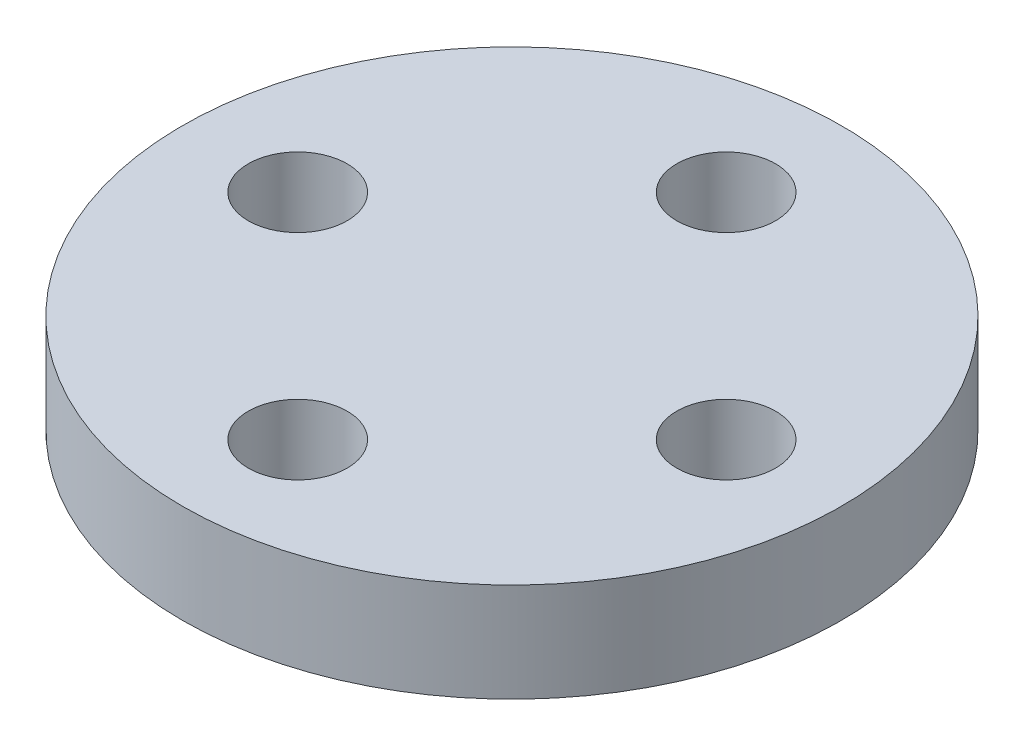
SolidWorks part; units mm, degrees
ref_plane "Front Plane" through (0, 0, 0) normal (0, 0, 1) x (1, 0, 0)
ref_plane "Top Plane" through (0, 0, 0) normal (0, 1, 0) x (1, 0, 0)
ref_plane "Right Plane" through (0, 0, 0) normal (1, 0, 0) x (0, 0, -1)
sketch "Sketch2" plane through (0, 0, 0) normal (0, 1, 0) x (1, 0, 0)
  circle A0 centre (0, 0) radius 10
  circle A7 centre (0, -6.5) radius 1.5
  circle A8 centre (-6.5, 0) radius 1.5
  circle A9 centre (0, 6.5) radius 1.5
  circle A10 centre (6.5, 0) radius 1.5
  dimension "D1" = 4
extrude "Boss-Extrude1" add sketch "Sketch2" along normal blind 3
sketch "Sketch3" plane through (0, 0, 0) normal (0, -1, 0) x (-1, 0, 0)
  circle A0 centre (0, 0) radius 4
extrude "Boss-Extrude2" add sketch "Sketch3" along normal blind 3
sketch "Sketch4" plane through (0, -3, 0) normal (0, -1, 0) x (1, 0, 0)
  circle A0 centre (0, 0) radius 1.5
extrude "Cut-Extrude1" cut sketch "Sketch4" against normal blind 3
